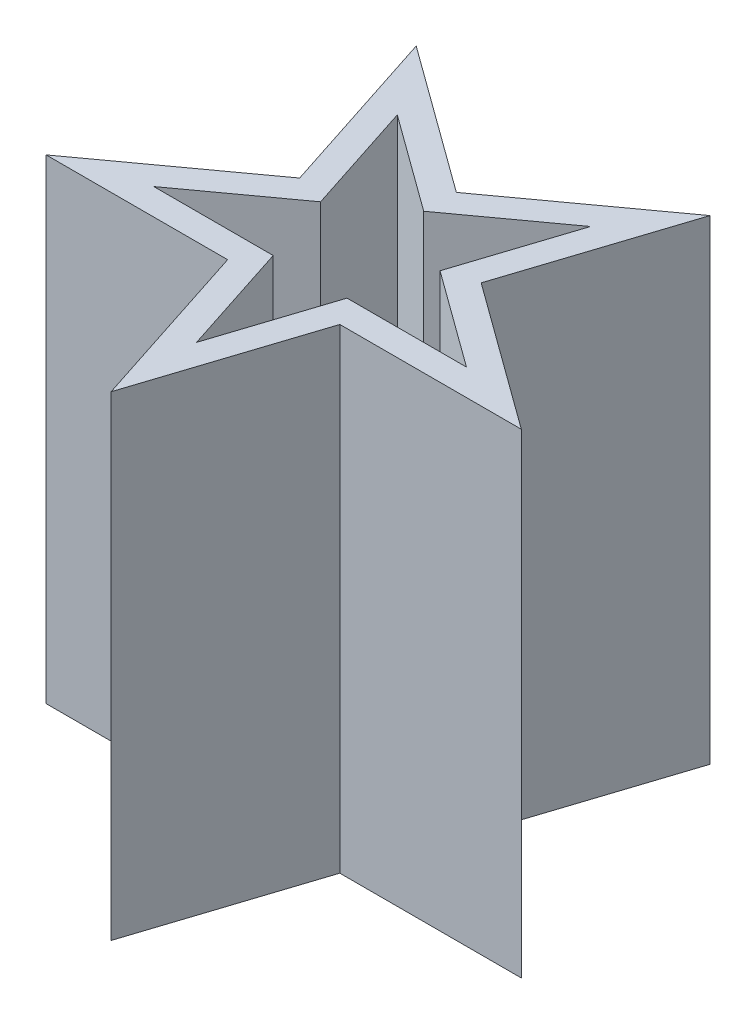
SolidWorks part; units mm, degrees
ref_plane "Front Plane" through (0, 0, 0) normal (0, 0, 1) x (1, 0, 0)
ref_plane "Top Plane" through (0, 0, 0) normal (0, 1, 0) x (1, 0, 0)
ref_plane "Right Plane" through (0, 0, 0) normal (1, 0, 0) x (0, 0, -1)
sketch "Sketch1" plane through (0, 0, 0) normal (0, 1, 0) x (1, 0, 0)
  line L0 (0, -2.9243) -> (0, -9.4632) construction
  line L16 (0, 3.6146) -> (-3.4377, 1.117) construction
  line L17 (-3.4377, 1.117) -> (-2.1246, -2.9243) construction
  line L18 (-2.1246, -2.9243) -> (2.1246, -2.9243) construction
  line L19 (2.1246, -2.9243) -> (3.4377, 1.117) construction
  line L20 (3.4377, 1.117) -> (0, 3.6146) construction
  line L21 (2.1246, -2.9243) -> (0, -9.4632)
  line L22 (0, -9.4632) -> (-2.1246, -2.9243)
  line L23 (-9, -2.9243) -> (-3.4377, 1.117)
  line L24 (-2.1246, -2.9243) -> (-9, -2.9243)
  line L25 (-5.5623, 7.6559) -> (0, 3.6146)
  line L26 (-3.4377, 1.117) -> (-5.5623, 7.6559)
  line L27 (5.5623, 7.6559) -> (3.4377, 1.117)
  line L28 (0, 3.6146) -> (5.5623, 7.6559)
  line L29 (9, -2.9243) -> (2.1246, -2.9243)
  line L30 (3.4377, 1.117) -> (9, -2.9243)
  circle A0 centre (0, 0) radius 2.9243 construction
  point P23 (0, 0)
  dimension "D1" = 18
extrude "Boss-Extrude1" add sketch "Sketch1" along normal blind 18
shell "Shell2" thickness 1
equation "\"L\" = 18"
equation "\"D1@Boss-Extrude1\"=\"L\""
equation "\"D1@Sketch1\"=\"L\""
